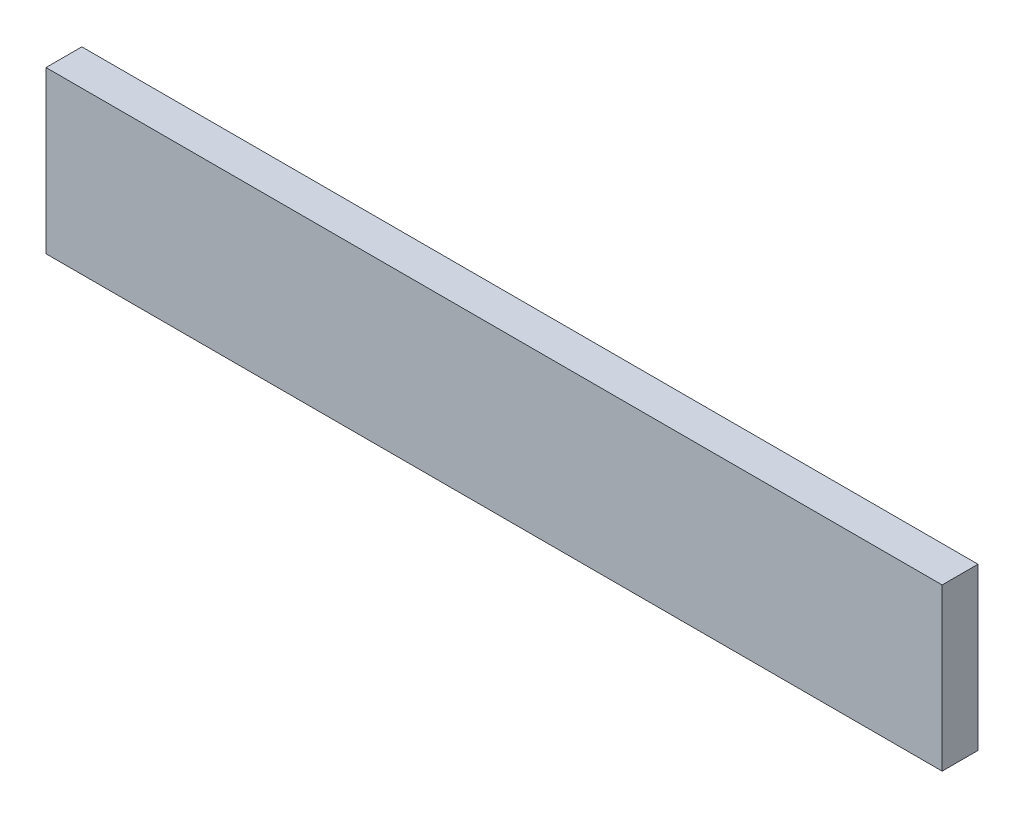
SolidWorks part; units mm, degrees
ref_plane "Front Plane" through (0, 0, 0) normal (0, 0, 1) x (1, 0, 0)
ref_plane "Top Plane" through (0, 0, 0) normal (0, 1, 0) x (1, 0, 0)
ref_plane "Right Plane" through (0, 0, 0) normal (1, 0, 0) x (0, 0, -1)
sketch "Sketch1" plane through (0, 0, 0) normal (0, 0, 1) x (1, 0, 0)
  line L1 (0, 0) -> (-250, 0)
  line L2 (0, 0) -> (0, 45)
  line L3 (0, 45) -> (-250, 45)
  line L4 (-250, 0) -> (-250, 45)
  dimension "D1" = 250
  dimension "D2" = 45
extrude "Boss-Extrude1" add sketch "Sketch1" along normal blind 10
